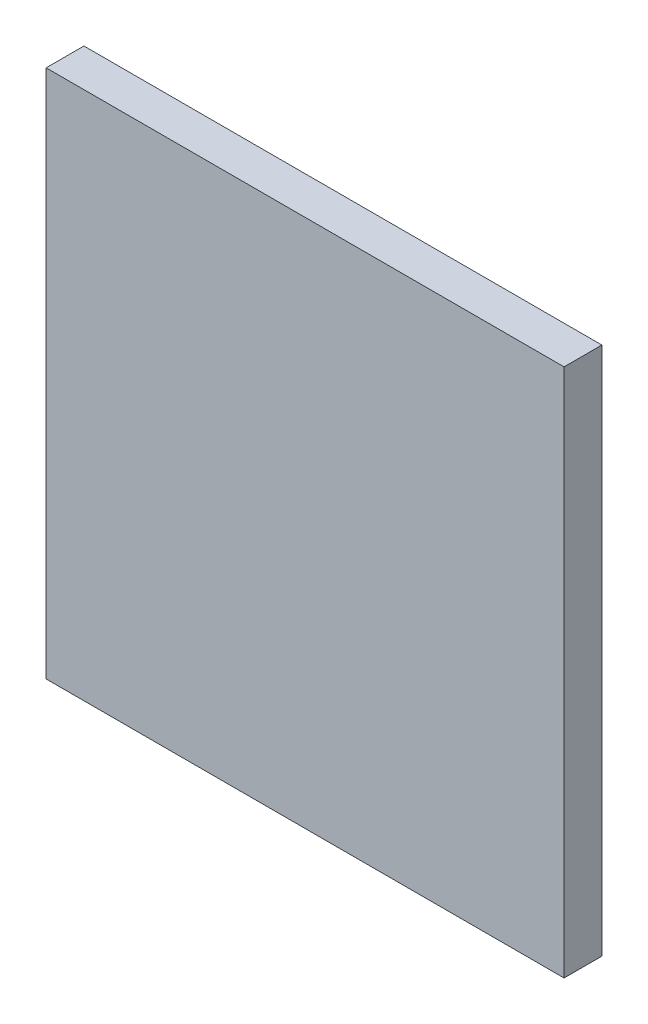
SolidWorks part; units mm, degrees
ref_plane "Front Plane" through (0, 0, 0) normal (1, 0, 0) x (0, 1, 0)
ref_plane "Top Plane" through (0, 0, 0) normal (0, 0, 1) x (0, 1, 0)
ref_plane "Right Plane" through (0, 0, 0) normal (0, 1, 0) x (-1, 0, 0)
sketch "Sketch1" plane through (0, 0, 0) normal (0, 0, 1) x (0, 1, 0)
  line L1 (70, 68.5) -> (-70, 68.5)
  line L2 (70, 68.5) -> (70, -68.5)
  line L3 (70, -68.5) -> (-70, -68.5)
  line L4 (-70, 68.5) -> (-70, -68.5)
  line L5 (70, 68.5) -> (-70, -68.5) construction
  line L6 (70, -68.5) -> (-70, 68.5) construction
  point P0 (0, 0)
  dimension "D1" = 140
  dimension "D2" = 137
extrude "Boss-Extrude1" add sketch "Sketch1" along normal blind 10
